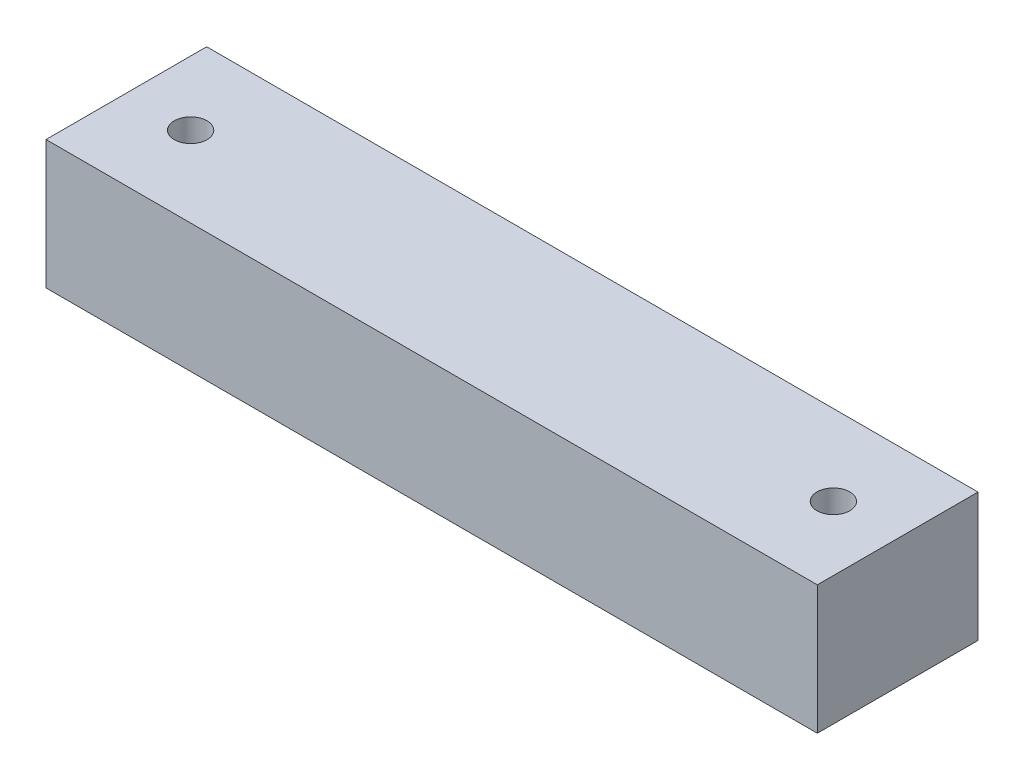
SolidWorks part; units mm, degrees
ref_plane "Front Plane" through (0, 0, 0) normal (0, 0, 1) x (1, 0, 0)
ref_plane "Top Plane" through (0, 0, 0) normal (0, 1, 0) x (1, 0, 0)
ref_plane "Right Plane" through (0, 0, 0) normal (1, 0, 0) x (0, 0, -1)
sketch "Sketch1" plane through (0, 0, 0) normal (0, 1, 0) x (1, 0, 0)
  line L1 (0, 0) -> (240, 0)
  line L2 (0, 0) -> (0, -50)
  line L3 (0, -50) -> (240, -50)
  line L4 (240, 0) -> (240, -50)
  dimension "D1" = 50
  dimension "D2" = 240
extrude "Boss-Extrude1" add sketch "Sketch1" along normal blind 40
hole_wizard "M12x1.75 Tapped Hole1" positions "Sketch2" profile "Sketch3" tap size "M12x1.75" standard "ANSI Metric"
sketch "Sketch2" plane through (0, 40, 0) normal (0, 1, 0) x (1, 0, 0)
  line L0 (0, 0) -> (0, -50) construction
  line L1 (0, -50) -> (240, -50) construction
  line L2 (240, -50) -> (240, 0) construction
  point P0 (20, -25)
  point P2 (220, -25)
  dimension "D1" = 20
  dimension "D2" = 25
  dimension "D3" = 20
sketch "Sketch3" plane through (20, 40, 25) normal (1, 0, 0) x (0, 0, 1)
  line L0 (0, 0) -> (0, 23.0644)
  line L1 (0, 23.0644) -> (5.1, 20)
  line L2 (5.1, 20) -> (5.1, 0)
  line L5 (5.1, 0) -> (0, 0)
  line L10 (0, 23.0644) -> (-5.1, 20) construction
  line L11 (0, -6.35) -> (0, 107.95) construction
  dimension "Tap Drill Dia." = 10.2
  dimension "Tap Drill Depth" = 20
  dimension "Drill Angle" = 118
cosmetic thread "Hole Thread1"
cosmetic thread "Hole Thread2"
